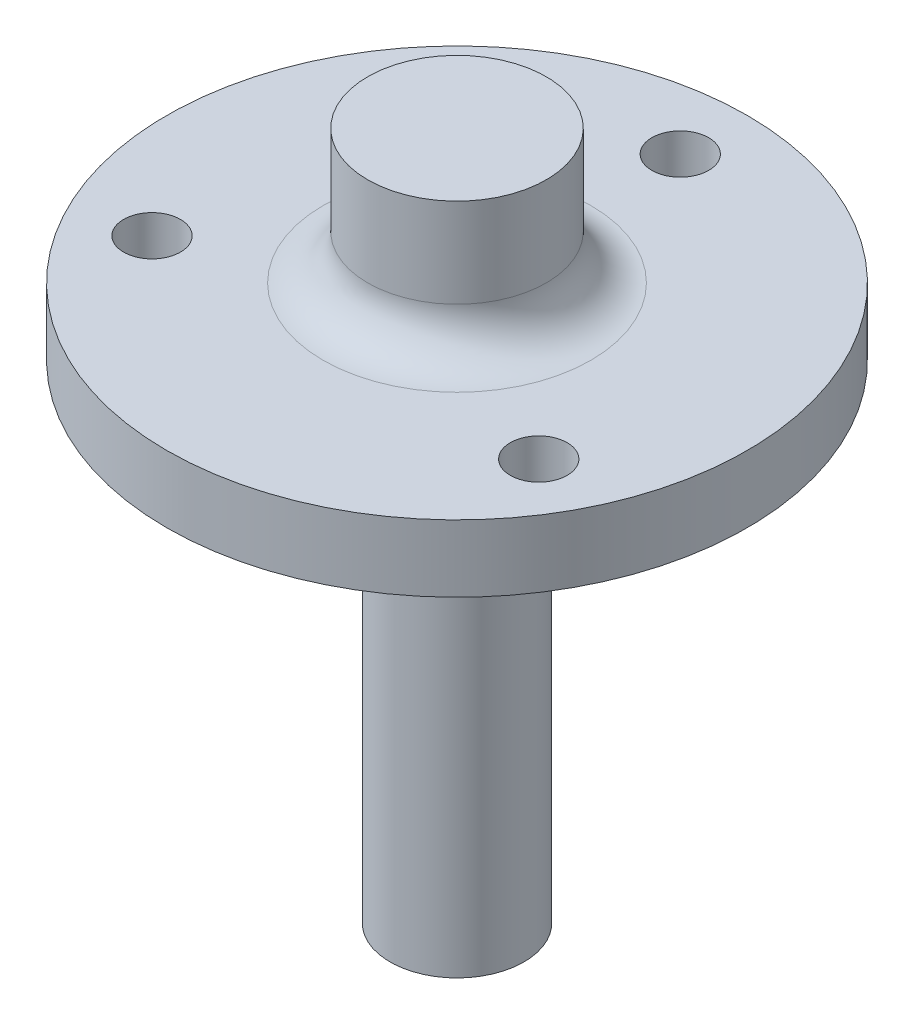
SolidWorks part; units mm, degrees
material "6061-T6 (SS)"
ref_plane "Front Plane" through (0, 0, 0) normal (0, 0, 1) x (1, 0, 0)
ref_plane "Top Plane" through (0, 0, 0) normal (0, 1, 0) x (1, 0, 0)
ref_plane "Right Plane" through (0, 0, 0) normal (1, 0, 0) x (0, 0, -1)
sketch "Sketch1" plane through (0, 0, 0) normal (0, 1, 0) x (1, 0, 0)
  circle A0 centre (0, 0) radius 20.6375
  point P0 (0, 0)
  dimension "D2" = 41.275
extrude "Boss-Extrude1" add sketch "Sketch1" along normal blind 4.7625
sketch "Sketch2" plane through (0, 0, 0) normal (0, -1, 0) x (1, 0, 0)
  circle A0 centre (0, 0) radius 8.7312
  dimension "D1" = 17.4625
extrude "Boss-Extrude2" add sketch "Sketch2" along normal blind 6.096
sketch "Sketch5" plane through (0, -6.096, 0) normal (0, -1, 0) x (1, 0, 0)
  circle A0 centre (0, 0) radius 4.7625
  dimension "D1" = 9.525
extrude "Boss-Extrude3" add sketch "Sketch5" along normal blind 28.575
hole_wizard "1/4-20 Tapped Hole2" positions "Sketch6" profile "Sketch7" tap size "1/4-20" standard "ANSI Inch"
sketch "Sketch6" plane through (0, -34.671, 0) normal (0, -1, 0) x (-1, 0, 0)
  point P0 (0, 0)
sketch "Sketch7" plane through (0, -34.671, 0) normal (1, 0, 0) x (0, 0, -1)
  line L0 (0, 0) -> (0, 30.7438)
  line L1 (0, 30.7438) -> (2.5527, 29.21)
  line L2 (2.5527, 29.21) -> (2.5527, 25.4)
  line L3 (2.5527, 25.4) -> (3.175, 25.4)
  line L4 (3.175, 25.4) -> (3.175, 0)
  line L5 (3.175, 0) -> (0, 0)
  line L10 (0, 30.7438) -> (-2.5527, 29.21) construction
  line L11 (0, -6.35) -> (0, 107.95) construction
  dimension "Tap Drill Dia." = 5.1054
  dimension "Tap Drill Depth" = 29.21
  dimension "Thread Major Dia." = 6.35
  dimension "Thread Depth" = 25.4
  dimension "Drill Angle" = 118
hole_wizard "#10-32 Tapped Hole1" positions "Sketch8" profile "Sketch10" tap size "#10-32" standard "ANSI Inch" end condition through all
sketch "Sketch8" plane through (0, 0, 0) normal (0, -1, 0) x (-1, 0, 0)
  line L1 (0, 15.875) -> (-13.7482, -7.9375)
  line L2 (-13.7482, -7.9375) -> (13.7482, -7.9375)
  line L3 (13.7482, -7.9375) -> (0, 15.875)
  circle A0 centre (0, 0) radius 7.9375 construction
  point P0 (-13.7482, -7.9375)
  point P2 (0, 15.875)
  point P4 (13.7482, -7.9375)
  dimension "D1" = 15.875
cosmetic thread "Hole Thread3" parameters "D2"=4.826
cosmetic thread "Hole Thread4" parameters "D2"=4.826
cosmetic thread "Hole Thread5" parameters "D2"=4.826
sketch "Sketch10" plane through (13.7482, 0, 7.9375) normal (1, 0, 0) x (0, 0, -1)
  line L0 (0, 0) -> (0, 4.7625)
  line L1 (0, 4.7625) -> (2.0193, 4.7625)
  line L2 (2.0193, 4.7625) -> (2.0193, 0)
  line L5 (2.0193, 0) -> (0, 0)
  line L11 (0, -6.35) -> (0, 107.95) construction
  dimension "Thru Tap Drill Dia." = 4.0386
  dimension "Thru Tap Drill Depth" = 4.7625
sketch "Sketch11" plane through (0, 4.7625, 0) normal (0, 1, 0) x (1, 0, 0)
  circle A0 centre (0, 0) radius 6.35
  dimension "D1" = 12.7
extrude "Boss-Extrude4" add sketch "Sketch11" along normal blind 9.525
fillet "Fillet1" radius 3.175 1 edges at (0, 4.7625, 6.35)
